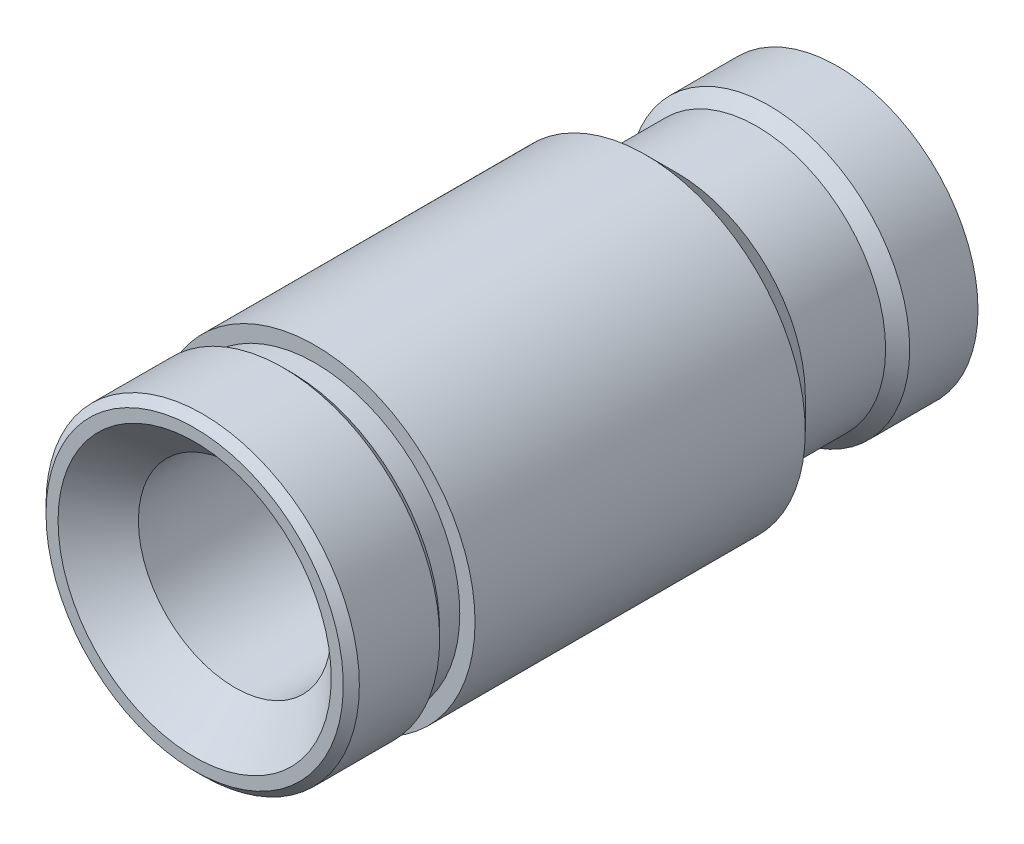
SolidWorks part; units mm, degrees
material "Latão"
ref_plane "Plano frontal" through (0, 0, 0) normal (0, 0, 1) x (1, 0, 0)
ref_plane "Plano superior" through (0, 0, 0) normal (0, 1, 0) x (1, 0, 0)
ref_plane "Plano direito" through (0, 0, 0) normal (1, 0, 0) x (0, 0, -1)
sketch "Esboço1" plane through (0, 0, 0) normal (1, 0, 0) x (0, 0, -1)
  line L0 (0.5, 12) -> (0.5, 19.5)
  line L1 (0.5, 19.5) -> (12.5, 19.5)
  line L2 (56.6, 19.9) -> (60.5, 16)
  line L3 (60.5, 16) -> (70.5, 16)
  line L4 (70.5, 16) -> (72, 17.5)
  line L5 (72, 17.5) -> (80.5, 17.5)
  line L6 (80.5, 17.5) -> (80.5, 12)
  line L7 (63.5, 12) -> (0.5, 12)
  line L8 (0, 0) -> (80, 0) construction
  line L9 (12.5, 19.5) -> (12.5, 18)
  line L10 (12.5, 18) -> (15.5, 18)
  line L11 (15.5, 18) -> (15.5, 19.9)
  line L12 (15.5, 19.9) -> (56.6, 19.9)
  line L13 (63.5, 12) -> (63.5, 11)
  line L14 (63.5, 11) -> (80.5, 11)
  line L15 (80.5, 11) -> (80.5, 12)
  point P3 (65.5, 16)
  dimension "D1" = 39
  dimension "D2" = 24
  dimension "D3" = 10
  dimension "D4" = 45
  dimension "D5" = 4
  dimension "D6" = 15
  dimension "D7" = 80
  dimension "D8" = 5.5
  dimension "D9" = 12
  dimension "D10" = 39.8
  dimension "D11" = 22
  dimension "D12" = 17
  dimension "D13" = 3
revolve "Revolução1" add sketch "Esboço1" angle 360 about L8
cosmetic thread "Representação de rosca1" parameters "D2"=35.704
cosmetic thread "Representação de rosca3" parameters "D1"=17, "D2"=24
ref_plane "Plano1" through (19.5, 0, 0) normal (1, 0, 0) x (0, 0, -1)
ref_plane "Plano2" through (0, 0, -40.5) normal (0, 0, -1) x (-1, 0, 0)
ref_plane "Plano3" through (30, 0, -30) normal (0.7071, 0, -0.7071) x (-0.7071, 0, -0.7071)
sketch "Esboço2" plane through (19.5, 0, 0) normal (1, 0, 0) x (0, 0, -1)
  line L1 (0.5, 19.5) -> (0.5, -19.5) construction
  line L2 (0.5, -20) -> (80, -20)
  line L3 (0.5, -20) -> (0.5, 20)
  line L4 (0.5, 20) -> (80, 20)
  line L5 (80, -20) -> (80, 20)
  line L6 (80, 0) -> (40, 0)
  line L7 (40, 20) -> (40, -20)
  dimension "D1" = 40
chamfer "Chanfro1" distance 1 angle 45 2 edges at (19.5, 0, -0.5) (19.5, 0, -12.5)
chamfer "Chanfro3" distance 2 angle 45 1 edges at (11, 0, -80.5)
chamfer "Chanfro4" distance 5 angle 45 1 edges at (12, 0, -0.5)
